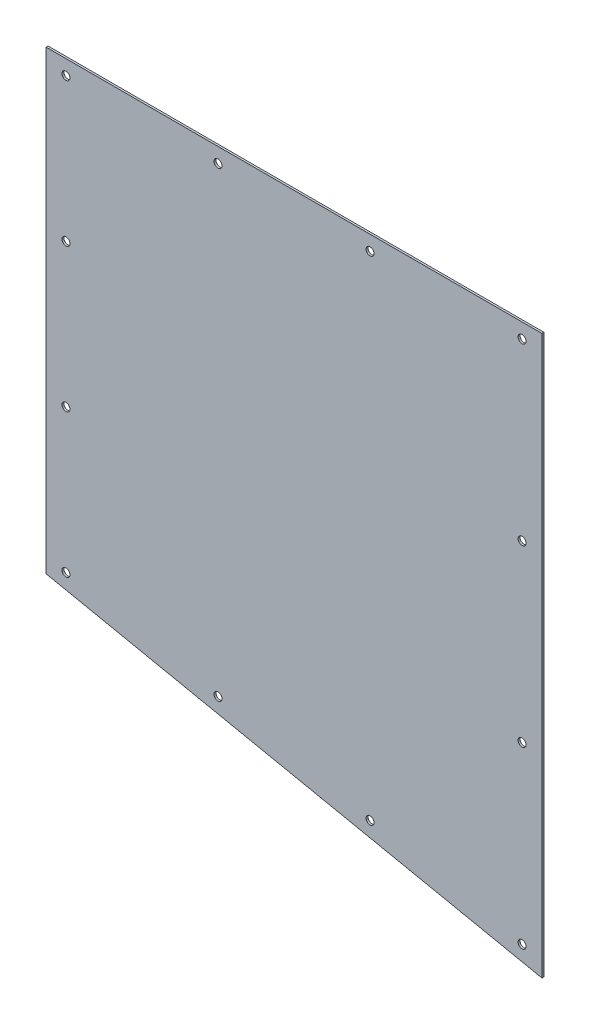
SolidWorks part; units mm, degrees
ref_plane "Plan de face" through (0, 0, 0) normal (0, 0, 1) x (1, 0, 0)
ref_plane "Plan de dessus" through (0, 0, 0) normal (0, 1, 0) x (1, 0, 0)
ref_plane "Plan de droite" through (0, 0, 0) normal (1, 0, 0) x (0, 0, -1)
sketch "Esquisse1" plane through (0, 0, 0) normal (0, 0, 1) x (1, 0, 0)
  line L1 (-250, 0) -> (250, 0)
  line L2 (-250, 0) -> (-250, -460)
  line L3 (-250, -460) -> (250, -563)
  line L4 (250, 0) -> (250, -563)
  dimension "D1" = 500
  dimension "D2" = 563
  dimension "D3" = 460
extrude "Boss.-Extru.1" add sketch "Esquisse1" along normal blind 2
sketch "Esquisse3" plane through (0, 0, 0) normal (0, 0, -1) x (-1, 0, 0)
  line L0 (-287.3276, -15) -> (291.8138, -15) construction
  line L1 (-276.3354, -553.1101) -> (276.909, -439.1418) construction
  line L2 (230, 19.3069) -> (230, -486.3281) construction
  line L3 (-230, 13.367) -> (-230, -576.1692) construction
  line L4 (-325.876, -197.7718) -> (785.876, -121.4315) construction
  line L5 (-306.4809, -377.8801) -> (305.9431, -293.7738) construction
  line L6 (-250, 0) -> (250, 0) construction
  line L7 (250, 0) -> (250, -460) construction
  line L8 (76.6667, 69.3135) -> (76.6667, -552.2261) construction
  line L9 (250, -460) -> (-250, -563) construction
  line L10 (-250, -563) -> (-250, 0) construction
  line L11 (-76.6667, 56.5857) -> (-76.6667, -576.1692) construction
  line L12 (230, -15) -> (230, -159.6017) construction
  line L13 (230, -159.6017) -> (230, -304.2034) construction
  line L14 (230, -304.2034) -> (230, -448.805) construction
  line L15 (-230, -15) -> (-230, -191.1883) construction
  line L16 (-230, -191.1883) -> (-230, -367.3767) construction
  line L17 (-230, -367.3767) -> (-230, -543.565) construction
  line L18 (-230, -15) -> (-76.6667, -15) construction
  line L19 (-76.6667, -15) -> (76.6667, -15) construction
  line L20 (76.6667, -15) -> (230, -15) construction
  circle A0 centre (-230, -15) radius 4
  circle A1 centre (-76.6667, -15) radius 4
  circle A2 centre (76.6667, -15) radius 4
  circle A3 centre (230, -15) radius 4
  circle A4 centre (230, -159.6017) radius 4
  circle A5 centre (230, -304.2034) radius 4
  circle A6 centre (423.4626, -408.9517) radius 4 construction
  circle A7 centre (76.6667, -480.3917) radius 4
  circle A8 centre (-76.6667, -511.9784) radius 4
  circle A9 centre (-230, -543.565) radius 4
  circle A10 centre (-230, -367.3767) radius 4
  circle A11 centre (-230, -191.1883) radius 4
  circle A12 centre (230, -448.805) radius 4
  point P20 (-230, -543.565)
  point P21 (423.4626, -408.9517)
  point P26 (230, -304.2034)
  point P27 (-230, -367.3767)
  point P28 (230, -159.6017)
  point P29 (-230, -191.1883)
  dimension "D15" = 8
  dimension "D16" = 8
  dimension "D17" = 4
  dimension "D18" = 4
  dimension "D19" = 8
  dimension "D20" = 4
  dimension "D21" = 4
  dimension "D22" = 4
  dimension "D23" = 4
  dimension "D24" = 4
  dimension "D25" = 4
  dimension "D26" = 8
  dimension "D28" = 8
  dimension "D1" = 15
  dimension "D2" = 20
  dimension "D3" = 15
  dimension "D4" = 20
  dimension "D5" = 528.565
  dimension "D6" = 460
  dimension "D7" = 433.805
  dimension "D14" = 220
extrude "Enlèv. mat.-Extru.1" cut sketch "Esquisse3" against normal blind 10
